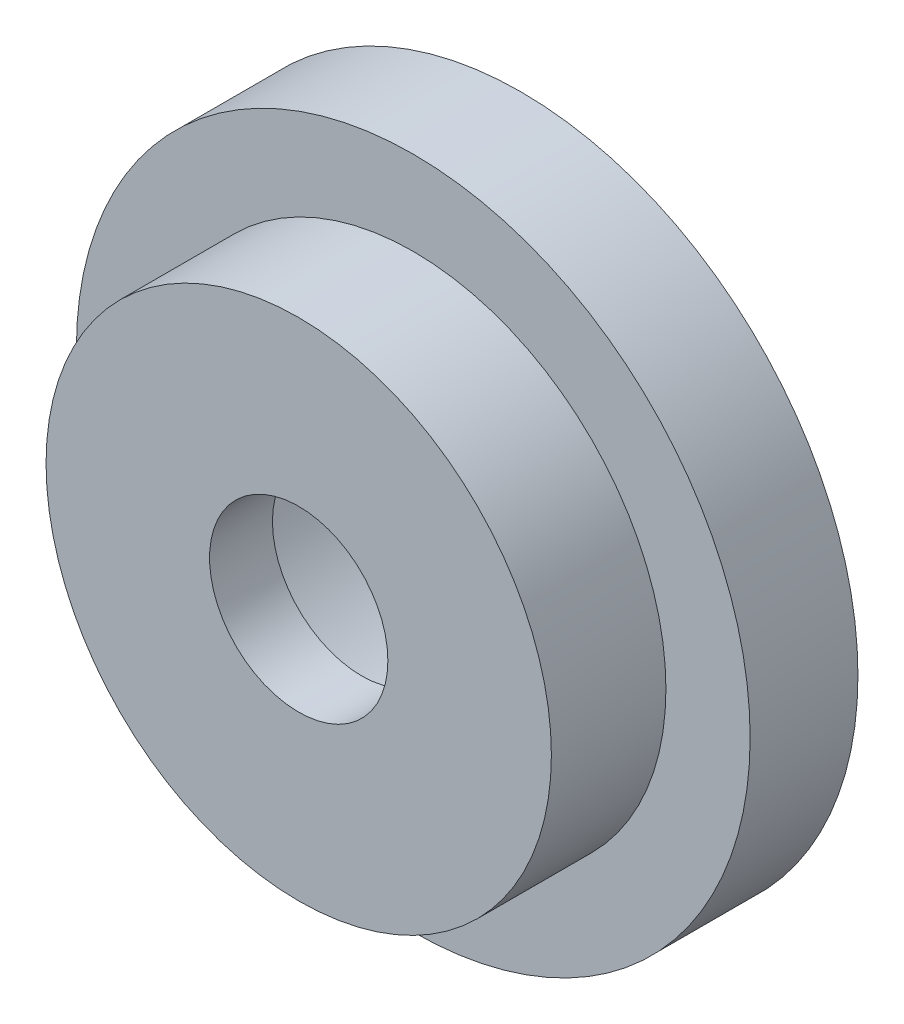
SolidWorks part; units mm, degrees
ref_plane "Front Plane" through (0, 0, 0) normal (0, 0, 1) x (1, 0, 0)
ref_plane "Top Plane" through (0, 0, 0) normal (0, 1, 0) x (1, 0, 0)
ref_plane "Right Plane" through (0, 0, 0) normal (1, 0, 0) x (0, 0, -1)
sketch "Sketch1" plane through (0, 0, 0) normal (1, 0, 0) x (0, 0, -1)
  line L0 (-13.6967, 0) -> (33.3737, 0) construction
  line L1 (0, 0) -> (0, 14.2875)
  line L2 (0, 14.2875) -> (6.477, 14.2875)
  line L3 (15.621, 14.2875) -> (15.621, 0)
  line L4 (15.621, 0) -> (0, 0)
  line L5 (6.477, 14.2875) -> (6.477, 19.05)
  line L6 (6.477, 19.05) -> (12.573, 19.05)
  line L7 (12.573, 19.05) -> (12.573, 14.2875)
  line L8 (12.573, 14.2875) -> (15.621, 14.2875)
  point P9 (9.525, 19.05)
  dimension "D1" = 14.2875
  dimension "D2" = 3.048
  dimension "D3" = 6.096
  dimension "D4" = 19.05
  dimension "D5" = 6.477
revolve "Revolve1" add sketch "Sketch1" angle 360 about L0
hole_wizard "3/8 Clearance Hole1" positions "Sketch2" profile "Sketch3" hole size "3/8" standard "ANSI Inch" end condition up to next
sketch "Sketch2" plane through (0, 0, 0) normal (0, 0, 1) x (1, 0, 0)
  point P0 (0, 0)
sketch "Sketch3" plane through (0, 0, 0) normal (1, 0, 0) x (0, -1, 0)
  line L0 (0, 0) -> (0, 15.621)
  line L1 (0, 15.621) -> (5.0419, 15.621)
  line L2 (5.0419, 15.621) -> (5.0419, 0)
  line L5 (5.0419, 0) -> (0, 0)
  line L11 (0, -6.35) -> (0, 107.95) construction
  dimension "Thru Hole Dia." = 10.0838
  dimension "Thru Hole Depth" = 15.621
sketch "Sketch6" plane through (0, 0, 0) normal (0, 0, 1) x (1, 0, 0)
  circle A0 centre (0, 0) radius 11.1125
  dimension "D1" = 22.225
extrude "Cut-Extrude1" [suppressed] cut sketch "Sketch6" against normal blind 7.112
sketch "Sketch7" plane through (0, 0, -15.621) normal (0, 0, -1) x (-1, 0, 0)
  circle A0 centre (0, 0) radius 11.1125
  dimension "D1" = 22.225
extrude "Cut-Extrude2" cut sketch "Sketch7" against normal blind 12.065
ref_plane "CenterPlane" through (0, 0, -9.525) normal (0, 0, 1) x (1, 0, 0)
